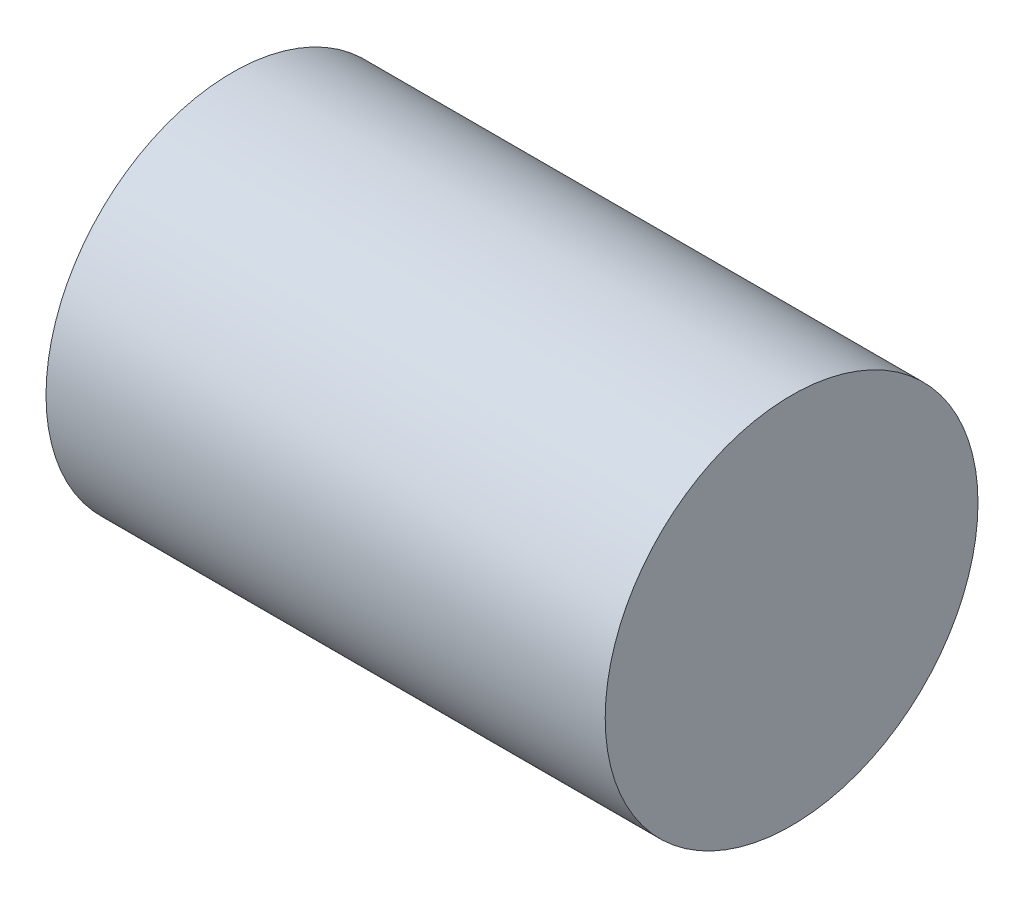
SolidWorks part; units mm, degrees
ref_plane "Front Plane" through (0, 0, 0) normal (0, 0, 1) x (1, 0, 0)
ref_plane "Top Plane" through (0, 0, 0) normal (0, 1, 0) x (1, 0, 0)
ref_plane "Right Plane" through (0, 0, 0) normal (1, 0, 0) x (0, 0, -1)
sketch "Sketch2" plane through (0, 0, 0) normal (1, 0, 0) x (0, 0, -1)
  circle A0 centre (0, 0) radius 5
  dimension "D1" = 10
extrude "Boss-Extrude1" add sketch "Sketch2" along normal blind 15
